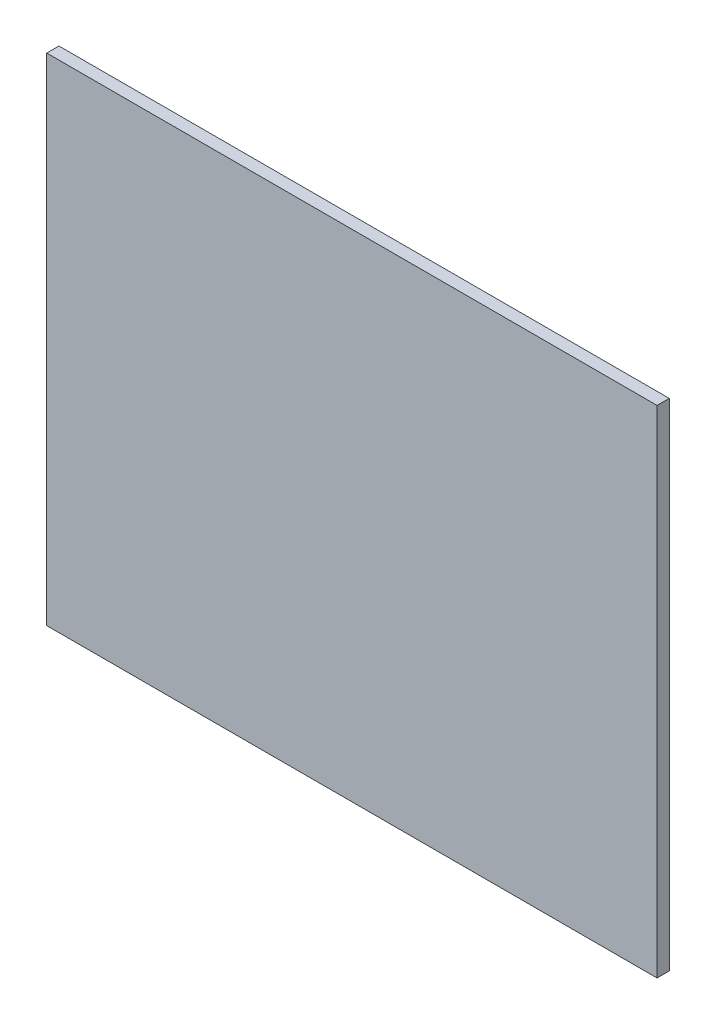
SolidWorks part; units mm, degrees
ref_plane "Front Plane" through (0, 0, 0) normal (0, 0, 1) x (1, 0, 0)
ref_plane "Top Plane" through (0, 0, 0) normal (0, 1, 0) x (1, 0, 0)
ref_plane "Right Plane" through (0, 0, 0) normal (1, 0, 0) x (0, 0, -1)
sketch "Sketch1" plane through (0, 0, 0) normal (0, 0, 1) x (1, 0, 0)
  line L1 (4.25, 70) -> (84.25, 70)
  line L3 (4.25, 5) -> (84.25, 5)
  line L4 (84.25, 70) -> (84.25, 5)
  line L5 (4.25, 70) -> (4.25, 5)
  dimension "D1" = 65
  dimension "D2" = 80
extrude "Boss-Extrude1" add sketch "Sketch1" along normal blind 1.6
